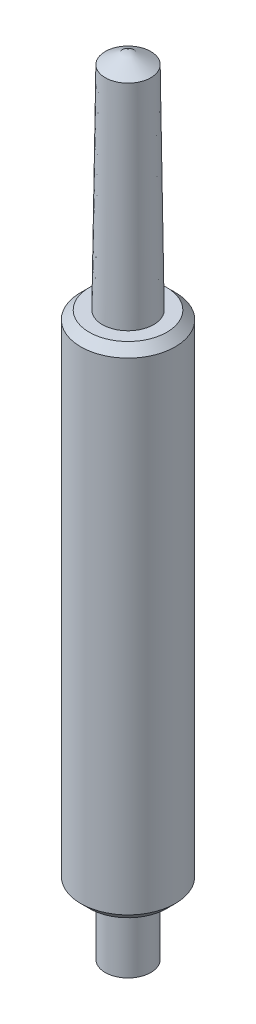
SolidWorks part; units mm, degrees
ref_plane "Alzado" through (0, 0, 0) normal (0, 0, 1) x (1, 0, 0)
ref_plane "Planta" through (0, 0, 0) normal (0, 1, 0) x (1, 0, 0)
ref_plane "Vista lateral" through (0, 0, 0) normal (1, 0, 0) x (0, 0, -1)
ref_plane "Plane1" through (0, 0, 0) normal (0, 0, -1) x (-1, 0, 0)
sketch "Sketch1" plane through (0, 0, 0) normal (0, 0, -1) x (-1, 0, 0)
  line L0 (-0.135, 0.0734) -> (0, 0)
  line L1 (0, -1000) -> (0, 49000) construction
  line L2 (-1000, 0) -> (49000, 0) construction
  line L3 (-0.28, 3.36) -> (-0.28, 0.5)
  line L4 (-0.28, 0.5) -> (-0.23, 0.45)
  line L5 (-0.23, 0.45) -> (-0.135, 0.45)
  line L6 (-0.135, 0.45) -> (-0.135, 0.0734)
  line L7 (-0.135, -999.9266) -> (-0.135, 49000.0734) construction
  line L8 (-0.28, -999.5) -> (-0.28, 49000.5) construction
  line L9 (-0.23, -999.55) -> (-0.23, 49000.45) construction
  line L10 (-1000.135, 0.0734) -> (48999.865, 0.0734) construction
  line L11 (-1000.135, 0.45) -> (48999.865, 0.45) construction
  line L12 (-1000.28, 0.5) -> (48999.72, 0.5) construction
  line L13 (-1000.28, 3.36) -> (48999.72, 3.36) construction
  line L14 (-998.4378, 3.41) -> (49001.5622, 3.41) construction
  line L15 (-0.28, 3.36) -> (-0.23, 3.41)
  line L16 (-998.4031, 4.67) -> (49001.5969, 4.67) construction
  line L17 (-998.4926, 4.75) -> (49001.5074, 4.75) construction
  line L18 (-0.152, -999.9266) -> (-0.152, 49000.0734) construction
  line L19 (0, 4.75) -> (-0.135, 4.67)
  line L20 (-0.135, 4.67) -> (-0.152, 3.41)
  line L21 (-0.152, 3.41) -> (-0.23, 3.41)
  line L22 (0, 4.75) -> (0, 0)
  point P32 (-0.152, 3.41)
  point P34 (-0.135, 4.67)
  point P35 (0, 4.75)
  dimension "D1" = 0.135
  dimension "D2" = 0.23
  dimension "D3" = 0.28
  dimension "D4" = 0.0734
  dimension "D5" = 0.45
  dimension "D6" = 0.5
  dimension "D7" = 3.36
  dimension "D8" = 3.41
  dimension "D9" = 4.67
  dimension "D10" = 4.75
  dimension "D11" = 0.152
revolve "Revolve1" add sketch "Sketch1" angle 360 about L1
